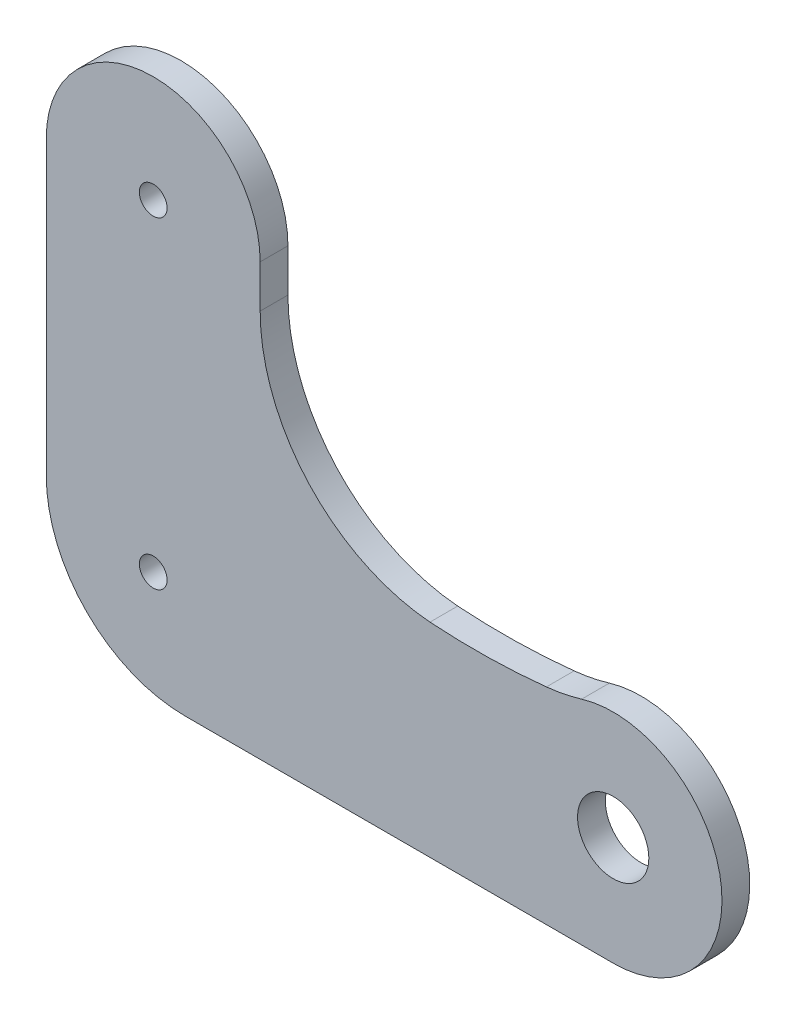
SolidWorks part; units mm, degrees
ref_plane "前基準面" through (0, 0, 0) normal (0, 0, 1) x (1, 0, 0)
ref_plane "上基準面" through (0, 0, 0) normal (0, 1, 0) x (1, 0, 0)
ref_plane "右基準面" through (0, 0, 0) normal (1, 0, 0) x (0, 0, -1)
sketch "草圖1" plane through (0, 0, 0) normal (0, 0, 1) x (1, 0, 0)
  line L4 (-1.0881, -16.7558) -> (45.1627, -16.7558)
  line L5 (7.023, 25.1901) -> (7.023, 29.7954)
  line L6 (-16.0881, 29.7954) -> (-16.0881, 20.3287)
  line L11 (-16.0881, 20.3287) -> (-16.0881, -1.7558)
  line L12 (45.1627, -5.0015) -> (41.7539, -5.0015) construction
  arc A29 (7.023, 29.7954) -> (-16.0881, 29.7954) centre (-4.5325, 29.7954) ccw
  circle A30 centre (-4.5325, 29.7954) radius 1.5
  circle A31 centre (45.1627, -5.0015) radius 3.85
  circle A32 centre (-4.5325, -5.0015) radius 1.5
  arc A33 (7.023, 25.1901) -> (25.3639, 5.259) centre (27.023, 25.1901) ccw
  arc A34 (45.1627, -16.7558) -> (41.7539, 6.2476) centre (45.1627, -5.0015) ccw
  arc A38 (25.3639, 5.259) -> (37.9457, 5.4875) centre (30.3408, 77.7238) ccw
  arc A39 (37.9457, 5.4875) -> (41.7539, 6.2476) centre (35.9537, 25.3881) ccw
  arc A40 (-16.0881, -1.7558) -> (-1.0881, -16.7558) centre (-1.0881, -1.7558) ccw
  point P13 (50.7874, -8)
  point P14 (-8, -8)
  point P15 (-8, 35.5617)
  dimension "D1" = 7.7
  dimension "D3" = 3
  dimension "D2" = 15
  dimension "D4" = 3
extrude "填料-伸長1" add sketch "草圖1" along normal blind 3 contours A38 A39 A34 L4 A40 L11 L6 A29 L5 A33 | A30 | A32 | A31
